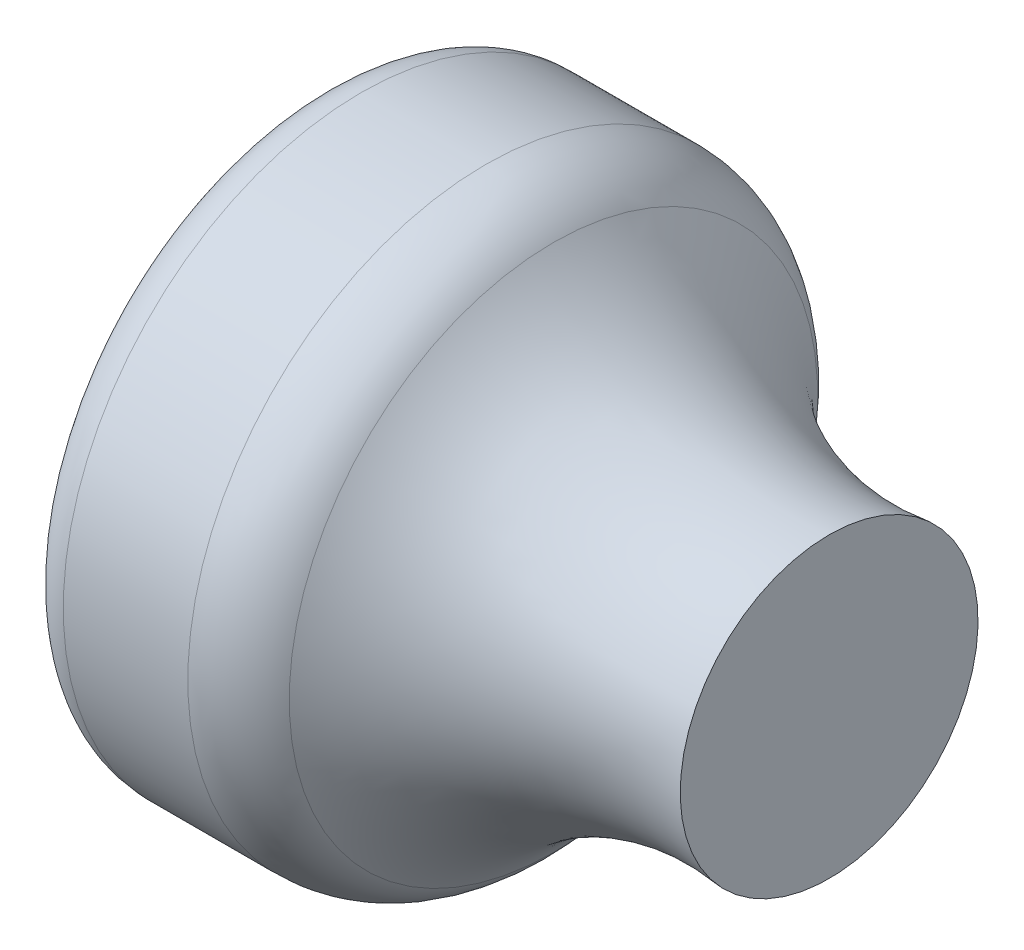
SolidWorks part; units mm, degrees
ref_plane "Front Plane" through (0, 0, 0) normal (0, 0, 1) x (1, 0, 0)
ref_plane "Top Plane" through (0, 0, 0) normal (0, 1, 0) x (1, 0, 0)
ref_plane "Right Plane" through (0, 0, 0) normal (1, 0, 0) x (0, 0, -1)
sketch "Sketch1" plane through (0, 0, 0) normal (0, 0, 1) x (1, 0, 0)
  line L0 (-12, 0) -> (-12, 6)
  line L1 (-11, 7) -> (-8.0731, 7)
  line L3 (0, 3.5) -> (0, 0)
  line L4 (0, 0) -> (-12, 0)
  arc A0 (0, 3.5) -> (-6.4801, 6.2092) centre (-0.9043, 10.4413) cw
  arc A1 (-12, 6) -> (-11, 7) centre (-11, 6) cw
  arc A2 (-8.0731, 7) -> (-6.4801, 6.2092) centre (-8.0731, 5) cw
  point P8 (-12, 7)
  point P11 (-7, 7)
  dimension "D5" = 1
  dimension "D6" = 2
  dimension "D7" = 7
  dimension "D1" = 3.5
  dimension "D2" = 7
  dimension "D3" = 12
  dimension "D4" = 5
  dimension "D8" = 0
revolve "Revolve1" add sketch "Sketch1" angle 360 about L4
